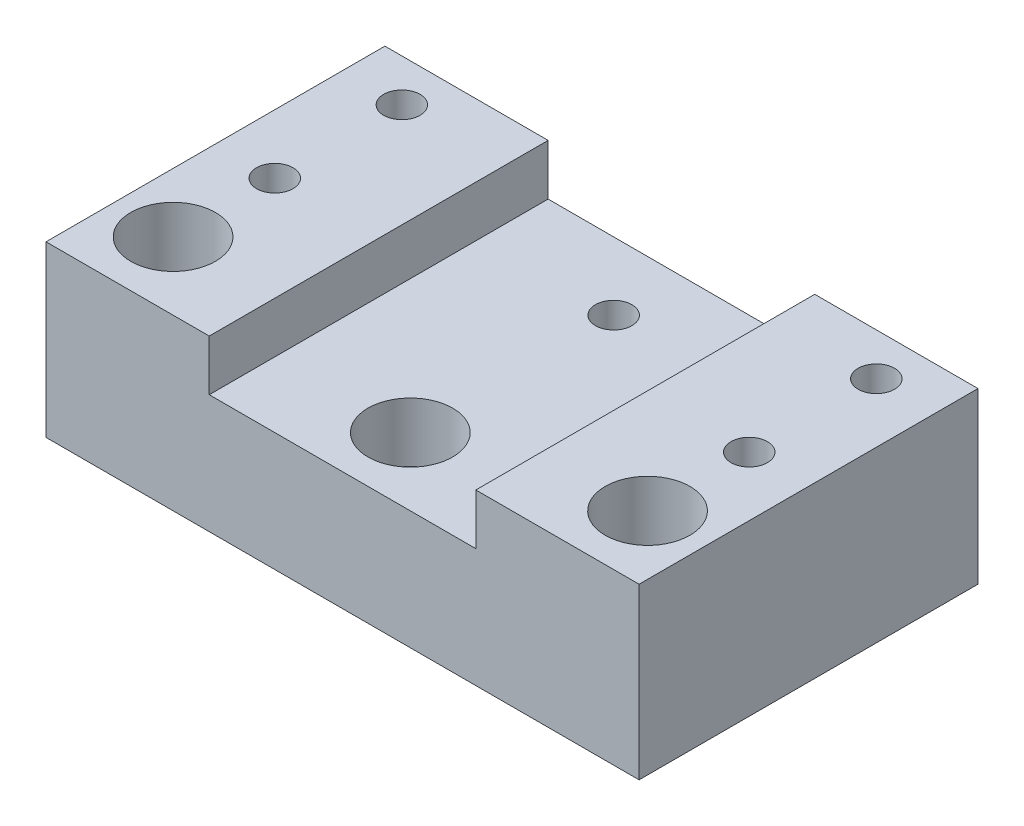
SolidWorks part; units mm, degrees
ref_plane "Ebene vorne" through (0, 0, 0) normal (0, 0, 1) x (1, 0, 0)
ref_plane "Ebene oben" through (0, 0, 0) normal (0, 1, 0) x (1, 0, 0)
ref_plane "Ebene rechts" through (0, 0, 0) normal (1, 0, 0) x (0, 0, -1)
sketch "Skizze1" plane through (0, 0, 0) normal (0, 0, 1) x (1, 0, 0)
  line L0 (-85.0721, 14.3687) -> (-15.0721, 14.3687)
  line L1 (-85.0721, 14.3687) -> (-85.0721, 34.3687)
  line L2 (-85.0721, 34.3687) -> (-65.8054, 34.3687)
  line L3 (-65.8054, 34.3687) -> (-65.8054, 28.3687)
  line L4 (-65.8054, 28.3687) -> (-34.3388, 28.3687)
  line L5 (-50.0721, 28.3687) -> (-50.0721, 14.3687)
  line L6 (-34.3388, 34.3687) -> (-34.3388, 28.3687)
  line L7 (-15.0721, 34.3687) -> (-34.3388, 34.3687)
  line L8 (-15.0721, 14.3687) -> (-15.0721, 34.3687)
  dimension "D1" = 20
  dimension "D2" = 70
  dimension "D3" = 6
extrude "Aufsatz-Linear austragen1" add sketch "Skizze1" along normal blind 40 contours L5 L4 L3 L2 L1 L0 | L0 L8 L7 L6 L4 L5
hole_wizard "Durchgangsloch für M41" positions "Skizze14" profile "Skizze15" hole size "M4" standard "ISO" end condition through all
sketch "Skizze14" plane through (0, 28.3687, 0) normal (0, 1, 0) x (1, 0, 0)
  line L0 (-15.0721, -40) -> (-15.0721, 0) construction
  line L1 (-65.8054, -40) -> (-34.3388, -40) construction
  point P0 (-50.0721, -8)
  dimension "D1" = 35
  dimension "D2" = 32
sketch "Skizze15" plane through (-50.0721, 28.3687, 8) normal (1, 0, 0) x (0, 0, 1)
  line L0 (0, 0) -> (0, 14)
  line L1 (0, 14) -> (2.15, 14)
  line L2 (2.15, 14) -> (2.15, 0)
  line L5 (2.15, 0) -> (0, 0)
  line L11 (0, -6.35) -> (0, 107.95) construction
  dimension "Bohrerdurchmesser" = 4.3
  dimension "Bohrungstiefe" = 14
hole_wizard "Durchgangsloch für M42" positions "Skizze16" profile "Skizze17" hole size "M4" standard "ISO" end condition through all
sketch "Skizze16" plane through (0, 34.3687, 0) normal (0, 1, 0) x (1, 0, 0)
  line L0 (-85.0721, -40) -> (-85.0721, 0) construction
  line L1 (-15.0721, -40) -> (-15.0721, 0) construction
  line L2 (-15.0721, 0) -> (-34.3388, 0) construction
  line L3 (-11, 0) -> (11, 0) construction
  point P0 (-78.0721, -5)
  point P2 (-78.0721, -20)
  point P4 (-22.0721, -20)
  point P6 (-22.0721, -5)
  dimension "D1" = 7
  dimension "D2" = 7
  dimension "D3" = 5
  dimension "D4" = 5
  dimension "D5" = 7
  dimension "D6" = 7
  dimension "D7" = 15
  dimension "D8" = 15
sketch "Skizze17" plane through (-78.0721, 34.3687, 5) normal (1, 0, 0) x (0, 0, 1)
  line L0 (0, 0) -> (0, 20)
  line L1 (0, 20) -> (2.15, 20)
  line L2 (2.15, 20) -> (2.15, 0)
  line L5 (2.15, 0) -> (0, 0)
  line L11 (0, -6.35) -> (0, 107.95) construction
  dimension "Bohrerdurchmesser" = 4.3
  dimension "Bohrungstiefe" = 20
sketch "Skizze20" plane through (0, 34.3687, 0) normal (0, 1, 0) x (1, 0, 0)
  line L0 (-85.0721, -40) -> (-85.0721, 0) construction
  line L1 (-15.0721, -40) -> (-15.0721, 0) construction
  line L2 (-15.0721, -40) -> (-34.3388, -40) construction
  line L3 (-85.0721, -40) -> (-65.8054, -40) construction
  point P0 (-78.0721, -32)
  point P2 (-22.0721, -32)
  dimension "D1" = 7
  dimension "D2" = 7
  dimension "D3" = 8
  dimension "D4" = 8
hole_wizard "Ø5.3 (5.3) Durchmesser Bohrung1" positions "Skizze20" profile "Skizze19" hole size "Ø5.3" standard "ISO" end condition through all
sketch "Skizze19" plane through (-78.0721, 34.3687, 32) normal (1, 0, 0) x (0, 0, 1)
  line L0 (0, 0) -> (0, 20)
  line L1 (0, 20) -> (2.65, 20)
  line L2 (2.65, 20) -> (2.65, 0)
  line L5 (2.65, 0) -> (0, 0)
  line L11 (0, -6.35) -> (0, 107.95) construction
  dimension "Bohrerdurchmesser" = 5.3
  dimension "Bohrungstiefe" = 20
sketch "Skizze23" plane through (0, 28.3687, 0) normal (0, 1, 0) x (1, 0, 0)
  line L0 (-15.0721, -40) -> (-15.0721, 0) construction
  line L1 (-65.8054, -40) -> (-34.3388, -40) construction
  point P0 (-50.0721, -32)
  dimension "D1" = 35
  dimension "D2" = 8
hole_wizard "Durchgangsloch für M81" positions "Skizze23" profile "Skizze22" hole size "M8" standard "ISO" end condition through all
sketch "Skizze22" plane through (-50.0721, 28.3687, 32) normal (1, 0, 0) x (0, 0, 1)
  line L0 (0, 0) -> (0, 14)
  line L1 (0, 14) -> (4.2, 14)
  line L2 (4.2, 14) -> (4.2, 0)
  line L5 (4.2, 0) -> (0, 0)
  line L11 (0, -6.35) -> (0, 107.95) construction
  dimension "Bohrerdurchmesser" = 8.4
  dimension "Bohrungstiefe" = 14
sketch "Skizze26" plane through (0, 34.3687, 0) normal (0, 1, 0) x (1, 0, 0)
  circle A0 centre (-78.0721, -32) radius 5
  circle A1 centre (-22.0721, -32) radius 5
extrude "Schnitt-Linear austragen3" cut sketch "Skizze26" against normal blind 12
sketch "Skizze27" plane through (0, 28.3687, 0) normal (0, 1, 0) x (1, 0, 0)
  circle A0 centre (-50.0721, -32) radius 5
extrude "Schnitt-Linear austragen4" cut sketch "Skizze27" against normal blind 7
